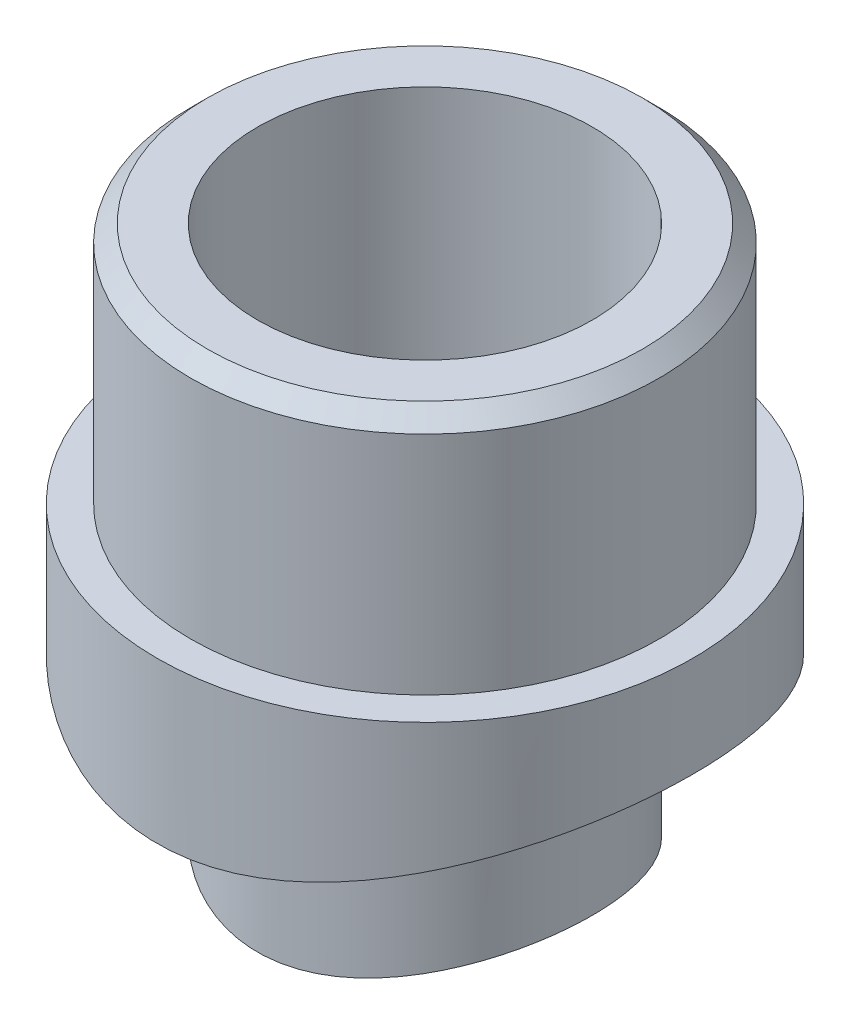
SolidWorks part; units mm, degrees
ref_plane "Front Plane" through (0, 0, 0) normal (0, 0, 1) x (1, 0, 0)
ref_plane "Top Plane" through (0, 0, 0) normal (0, 1, 0) x (1, 0, 0)
ref_plane "Right Plane" through (0, 0, 0) normal (1, 0, 0) x (0, 0, -1)
sketch "Sketch1" plane through (0, 0, 0) normal (0, 1, 0) x (1, 0, 0)
  circle A0 centre (0, 0) radius 16
  circle A1 centre (0, 0) radius 6.6
  dimension "D1" = 32
  dimension "D2" = 13.2
extrude "Boss-Extrude1" add sketch "Sketch1" along normal blind 43.5
sketch "Sketch2" plane through (0, 43.5, 0) normal (0, 1, 0) x (1, 0, 0)
  circle A0 centre (0, 0) radius 14
  circle A1 centre (0, 0) radius 10
  dimension "D1" = 28
  dimension "D2" = 20
extrude "Boss-Extrude2" add sketch "Sketch2" along normal blind 14.5
sketch "Sketch3" plane through (0, 0, 0) normal (1, 0, 0) x (0, 0, -1)
  circle A0 centre (0, 0) radius 37.5
  dimension "D1" = 75
extrude "Cut-Extrude1" cut sketch "Sketch3" against normal through all both and the other way through all
sketch "Sketch4" plane through (0, 0, 0) normal (0, 1, 0) x (1, 0, 0)
  circle A0 centre (0, 0) radius 6.6
  circle A1 centre (0, 0) radius 10
extrude "Boss-Extrude3" add sketch "Sketch4" along normal up to next
sketch "Sketch5" plane through (0, 0, 0) normal (1, 0, 0) x (0, 0, -1)
  circle A0 centre (0, 0) radius 27.2
  dimension "D1" = 54.4
extrude "Cut-Extrude2" cut sketch "Sketch5" against normal through all both and the other way through all
chamfer "Chamfer1" distance 1 angle 45 1 edges at (0, 58, 14)
